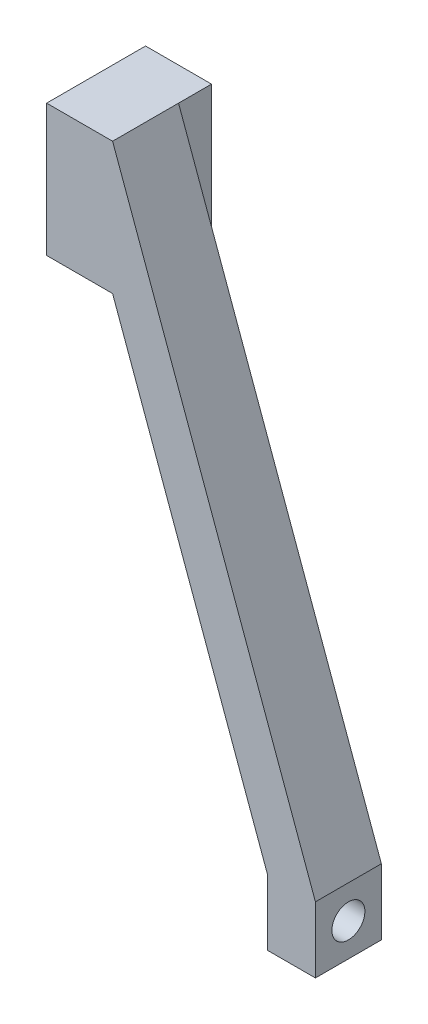
SolidWorks part; units mm, degrees
ref_plane "Front Plane" through (0, 0, 0) normal (0, 0, 1) x (1, 0, 0)
ref_plane "Top Plane" through (0, 0, 0) normal (0, 1, 0) x (1, 0, 0)
ref_plane "Right Plane" through (0, 0, 0) normal (1, 0, 0) x (0, 0, -1)
sketch "Sketch1" plane through (0, 0, 0) normal (0, 0, 1) x (1, 0, 0)
  line L0 (0, 0) -> (0, 25.4)
  line L1 (0, 25.4) -> (12.7, 25.4)
  line L2 (0, 0) -> (12.7, 0)
  line L3 (12.7, 0) -> (42.5092, -81.9)
  line L4 (42.5092, -94.6) -> (51.754, -94.6)
  line L5 (51.754, -94.6) -> (51.754, -81.9)
  line L6 (42.5092, -81.9) -> (42.5092, -94.6)
  line L7 (51.754, -81.9) -> (12.7, 25.4)
  dimension "D1" = 25.4
  dimension "D2" = 120
  dimension "D3" = 12.7
  dimension "D4" = 70
  dimension "D5" = 12.7
  dimension "D6" = 12.7
extrude "Boss-Extrude1" add sketch "Sketch1" against normal blind 12.7
sketch "Sketch2" plane through (42.5092, 0, 0) normal (-1, 0, 0) x (0, 0, 1)
  line L1 (-12.7, -81.9) -> (-12.7, -94.6) construction
  line L2 (-12.7, -81.9) -> (0, -81.9) construction
  circle A1 centre (-6.35, -88.25) radius 3.175
  point P4 (-12.7, -88.25)
  point P7 (-6.35, -81.9)
  dimension "D1" = 3.175
extrude "Cut-Extrude1" cut sketch "Sketch2" against normal through all
sketch "Sketch5" plane through (0, 0, -12.7) normal (0, 0, 1) x (1, 0, 0)
  line L0 (12.7, 25.4) -> (0, 25.4)
  line L1 (0, 25.4) -> (0, 0)
  line L2 (0, 0) -> (12.7, 0)
  line L4 (12.7, 0) -> (12.7, 25.4)
  line L5 (12.7, 0) -> (42.5092, -81.9) construction
extrude "Boss-Extrude2" add sketch "Sketch5" against normal blind 6.35
sketch "Sketch4" plane through (0, 0, 0) normal (0, -1, 0) x (1, 0, 0)
  line L0 (0, -12.7) -> (12.7, -12.7) construction
  line L3 (42.5092, -12.7) -> (42.5092, 0) construction
  circle A0 centre (6.35, -12.7) radius 3.175
  point P4 (6.35, -12.7)
  point P8 (42.5092, -6.35)
  dimension "D1" = 6.35
  dimension "D2" = 6.35
extrude "Cut-Extrude2" cut sketch "Sketch4" against normal blind 19.05
